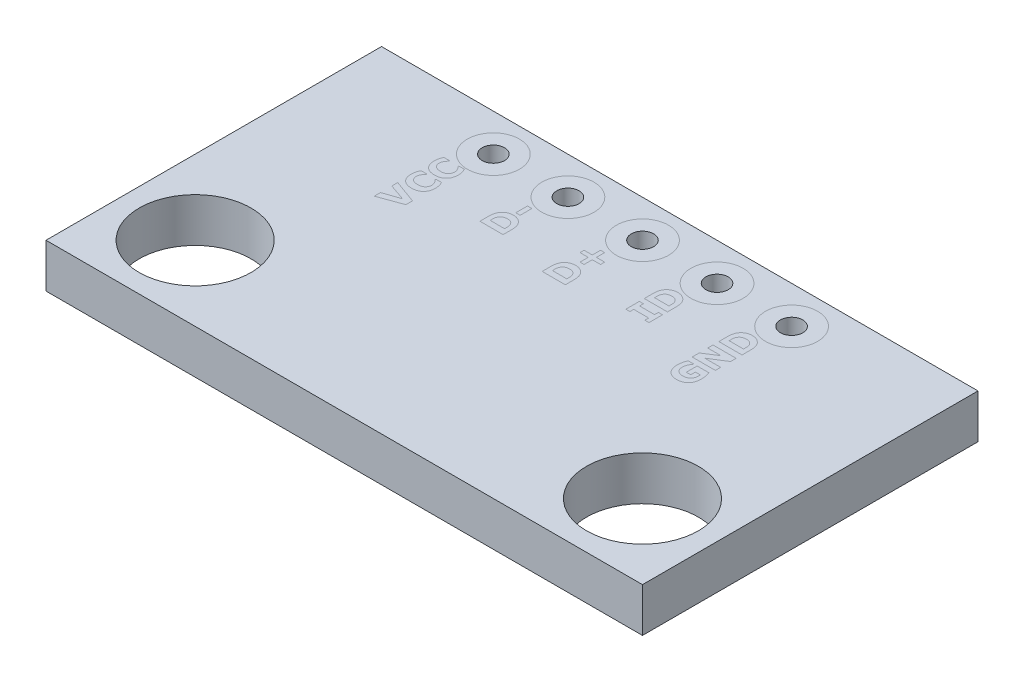
SolidWorks part; units mm, degrees
ref_plane "정면" through (0, 0, 0) normal (0, 0, 1) x (1, 0, 0)
ref_plane "윗면" through (0, 0, 0) normal (0, 1, 0) x (1, 0, 0)
ref_plane "우측면" through (0, 0, 0) normal (1, 0, 0) x (0, 0, -1)
sketch "스케치1" plane through (0, 0, 0) normal (0, 1, 0) x (1, 0, 0)
  line L0 (-7.62, -3.175) -> (7.62, -3.175) construction
  line L1 (-10.16, -5.715) -> (10.16, -5.715)
  line L2 (-10.16, -5.715) -> (-10.16, 5.715)
  line L3 (-10.16, 5.715) -> (10.16, 5.715)
  line L4 (10.16, -5.715) -> (10.16, 5.715)
  line L5 (-10.16, -5.715) -> (10.16, 5.715) construction
  line L6 (-10.16, 5.715) -> (10.16, -5.715) construction
  line L7 (0, 5.715) -> (0, -5.715) construction
  line L8 (-10.16, 4.445) -> (10.16, 4.445) construction
  circle A0 centre (-7.62, -3.175) radius 1.905
  circle A1 centre (7.62, -3.175) radius 1.905
  circle A2 centre (5.08, 4.445) radius 0.381
  circle A3 centre (2.54, 4.445) radius 0.381
  circle A4 centre (-2.54, 4.445) radius 0.381
  circle A5 centre (-5.08, 4.445) radius 0.381
  circle A6 centre (0, 4.445) radius 0.381
  point P0 (0, 0)
  dimension "D3" = 15.24
  dimension "D5" = 3.81
  dimension "D7" = 0.762
  dimension "D1" = 11.43
  dimension "D2" = 20.32
  dimension "D4" = 2.54
  dimension "D6" = 1.27
  dimension "D8" = 2.54
  dimension "D9" = 2.54
extrude "보스-돌출1" add sketch "스케치1" along normal blind 1.5
sketch "스케치2" plane through (0, 1.5, 0) normal (0, 1, 0) x (1, 0, 0)
  circle A0 centre (5.08, 4.445) radius 0.889
  circle A1 centre (2.54, 4.445) radius 0.889
  circle A2 centre (0, 4.445) radius 0.889
  circle A3 centre (-2.54, 4.445) radius 0.889
  circle A4 centre (-5.08, 4.445) radius 0.889
  dimension "D1" = 1.778
split line "분할선1"
sketch "스케치3" plane through (0, 1.5, 0) normal (0, 1, 0) x (1, 0, 0)
  line L0 (-5.08, 4.445) -> (-5.08, 3.556) construction
  line L1 (-10.16, -5.715) -> (10.16, -5.715) construction
  line L2 (-2.54, 4.445) -> (-2.54, 3.556) construction
  line L3 (0, 4.445) -> (0, 3.556) construction
  line L4 (2.54, 4.445) -> (2.54, 3.556) construction
  line L5 (5.08, 4.445) -> (5.08, 3.556) construction
  line L6 (10.16, 3.556) -> (-10.16, 3.556) construction
  line L7 (10.16, -5.715) -> (10.16, 5.715) construction
  line L8 (-10.16, 5.715) -> (-10.16, -5.715) construction
  line L9 (5.08, 3.556) -> (5.08, -5.715) construction
  line L10 (2.54, 3.556) -> (2.54, -5.715) construction
  line L11 (0, 3.556) -> (0, -5.715) construction
  line L12 (-2.54, 3.556) -> (-2.54, -5.715) construction
  line L13 (-5.08, 3.556) -> (-5.08, -5.715) construction
  circle A0 centre (5.08, 4.445) radius 0.889 construction
  text T0 "VCC" font "Verdana" height in points 3
  text T1 "D-" font "Verdana" height in points 3
  text T2 "D+" font "Verdana" height in points 3
  text T3 "ID" font "Verdana" height in points 3
  text T4 "GND" font "Verdana" height in points 3
  point P25 (-5.08, 3.1583)
  point P31 (0, 0)
  point P32 (0, 0)
split line "분할선2"
